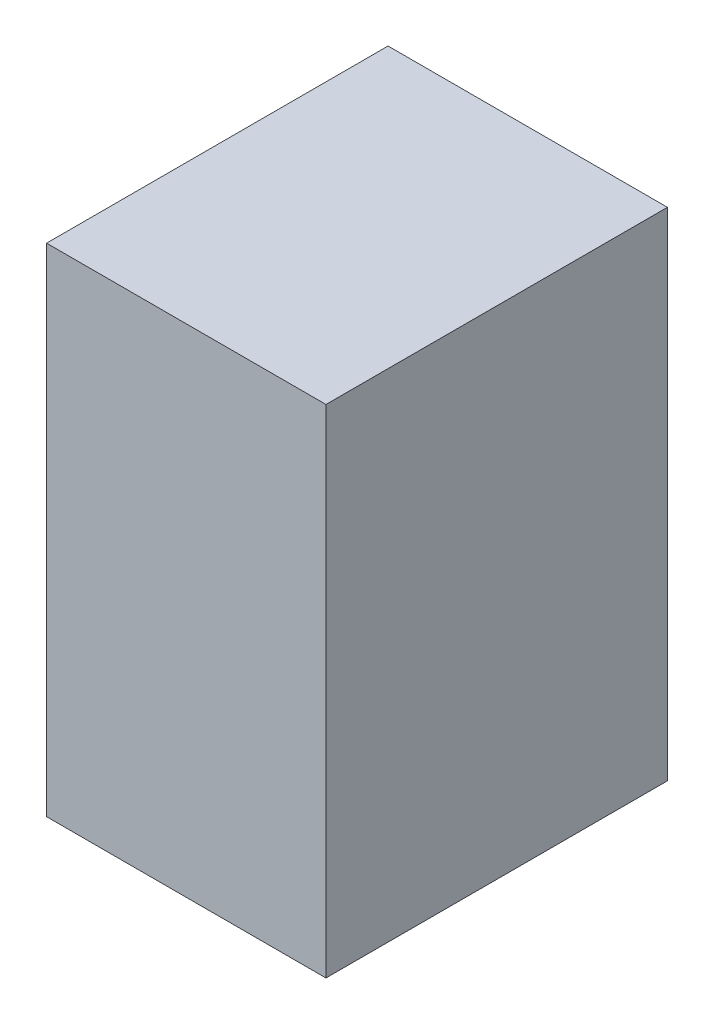
SolidWorks part; units mm, degrees
ref_plane "Спереди" through (0, 0, 0) normal (0, 0, 1) x (1, 0, 0)
ref_plane "Сверху" through (0, 0, 0) normal (0, 1, 0) x (1, 0, 0)
ref_plane "Справа" through (0, 0, 0) normal (1, 0, 0) x (0, 0, -1)
sketch "Эскиз1" plane through (0, 0, 0) normal (0, 1, 0) x (1, 0, 0)
  line L1 (0, 0) -> (450, 0)
  line L2 (0, 0) -> (0, 550)
  line L3 (0, 550) -> (450, 550)
  line L4 (450, 0) -> (450, 550)
extrude "Бобышка-Вытянуть1" add sketch "Эскиз1" along normal blind 800
